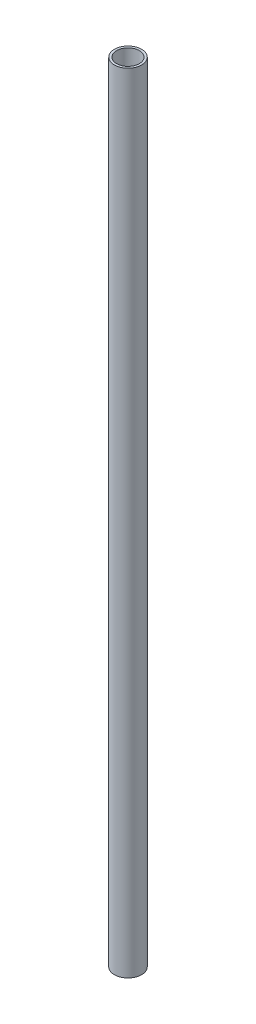
SolidWorks part; units mm, degrees
ref_plane "Front Plane" through (0, 0, 0) normal (0, 0, 1) x (1, 0, 0)
ref_plane "Top Plane" through (0, 0, 0) normal (0, 1, 0) x (1, 0, 0)
ref_plane "Right Plane" through (0, 0, 0) normal (1, 0, 0) x (0, 0, -1)
sketch "Sketch1" plane through (0, 0, 0) normal (0, 1, 0) x (1, 0, 0)
  circle A0 centre (0, 0) radius 6
  circle A1 centre (0, 0) radius 5
  dimension "D1" = 1
  dimension "D2" = 12
extrude "Boss-Extrude1" add sketch "Sketch1" along normal blind 347
